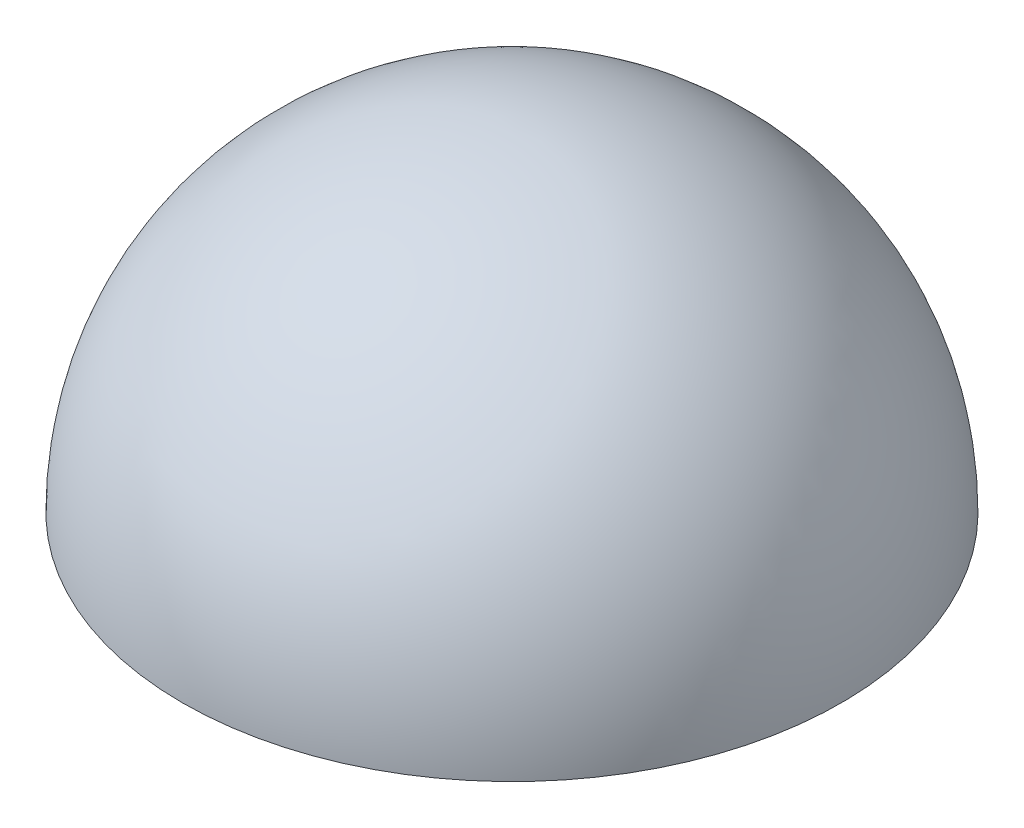
SolidWorks part; units mm, degrees
ref_plane "Front Plane" through (0, 0, 0) normal (0, 0, 1) x (1, 0, 0)
ref_plane "Top Plane" through (0, 0, 0) normal (0, 1, 0) x (1, 0, 0)
ref_plane "Right Plane" through (0, 0, 0) normal (1, 0, 0) x (0, 0, -1)
sketch "Sketch1" plane through (0, 0, 0) normal (0, 1, 0) x (1, 0, 0)
  line L0 (0, -4) -> (0, 4)
  arc A0 (0, 4) -> (0, -4) centre (0, 0) ccw
revolve "Revolve1" add sketch "Sketch1" angle 180 about L0
